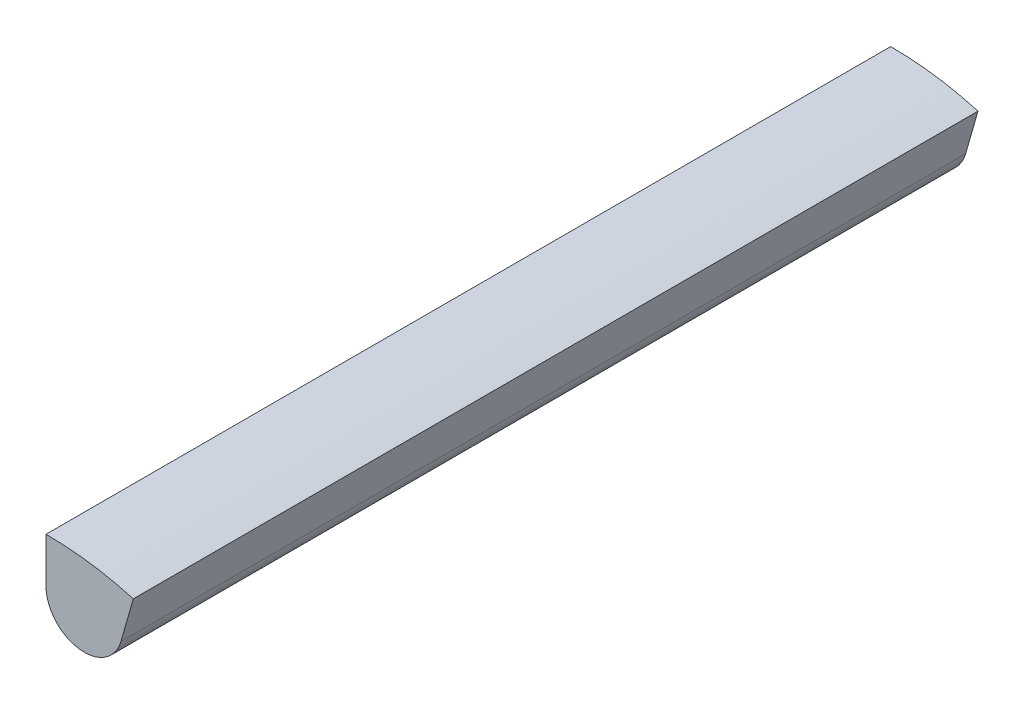
SolidWorks part; units mm, degrees
ref_plane "Front Plane" through (0, 0, 0) normal (0, 0, 1) x (1, 0, 0)
ref_plane "Top Plane" through (0, 0, 0) normal (0, 1, 0) x (1, 0, 0)
ref_plane "Right Plane" through (0, 0, 0) normal (1, 0, 0) x (0, 0, -1)
sketch "Sketch1" plane through (0, 0, 0) normal (0, 0, 1) x (1, 0, 0)
  line L0 (0, 0) -> (0, 37.5)
  line L1 (0, 0) -> (10.3364, 36.0473)
  line L2 (0, 0) -> (5.219, 37.1351)
  circle A0 centre (0, 0) radius 37.5
  circle A1 centre (4.5231, 32.1837) radius 4.5231
  dimension "D1" = 75
  dimension "D2" = 16
  dimension "D3" = 8
  dimension "D4" = 5
extrude "Boss-Extrude1" add sketch "Sketch1" along normal blind 100 contours L2 A1 | L2 A1 | A1 L1 A0 L2 | A1 L2 A0 L0
